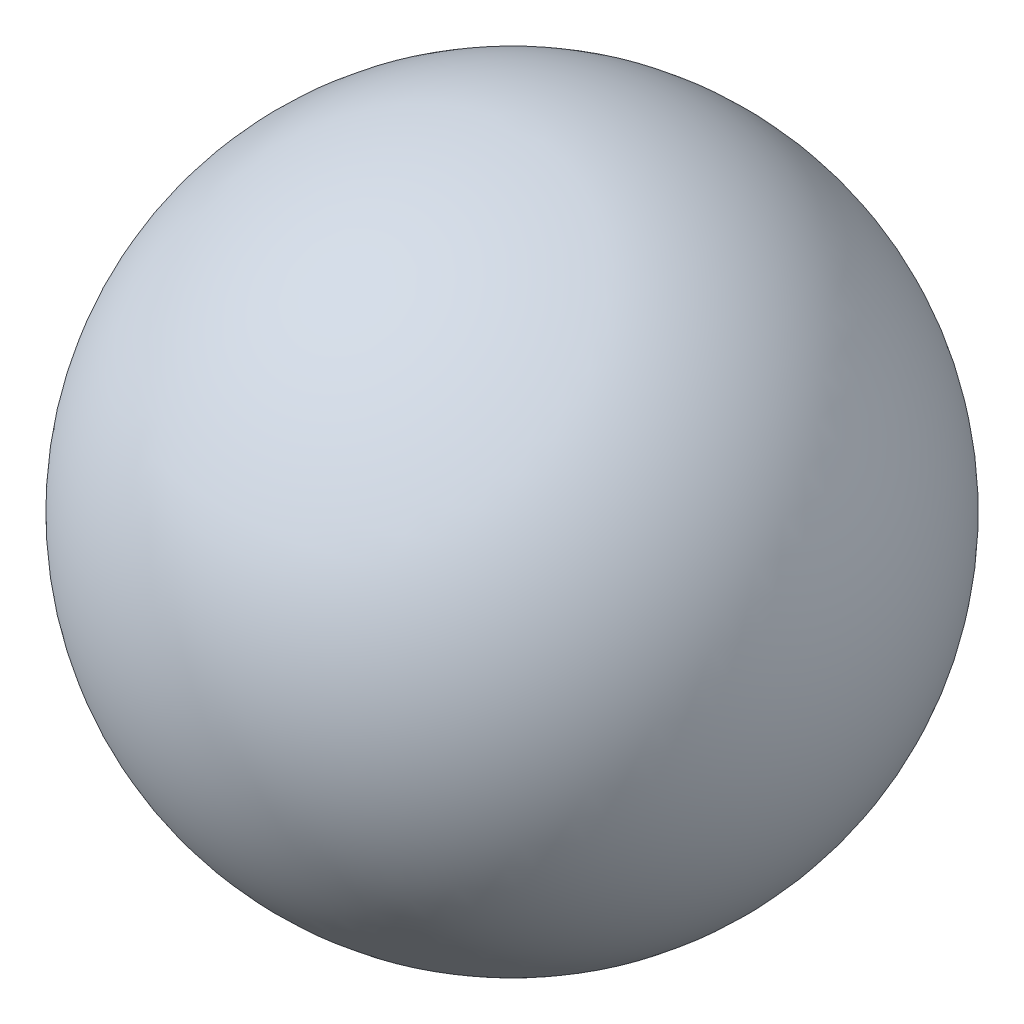
SolidWorks part; units mm, degrees
ref_plane "Front Plane" through (0, 0, 0) normal (0, 0, 1) x (1, 0, 0)
ref_plane "Top Plane" through (0, 0, 0) normal (0, 1, 0) x (1, 0, 0)
ref_plane "Right Plane" through (0, 0, 0) normal (1, 0, 0) x (0, 0, -1)
sketch "Sketch1" plane through (0, 0, 0) normal (0, 0, 1) x (1, 0, 0)
  line L0 (0, 34.1) -> (0, -34.1) construction
  line L1 (0, 34.1) -> (0, 36.5)
  line L2 (0, -34.1) -> (0, -36.5)
  arc A0 (0, 34.1) -> (0, -34.1) centre (0, 0) cw
  arc A1 (0, 36.5) -> (0, -36.5) centre (0, 0) cw
  point P4 (0, 0)
  dimension "D1" = 36.5
  dimension "D2" = 2.4
revolve "Revolve1" add sketch "Sketch1" angle 360 about L0
